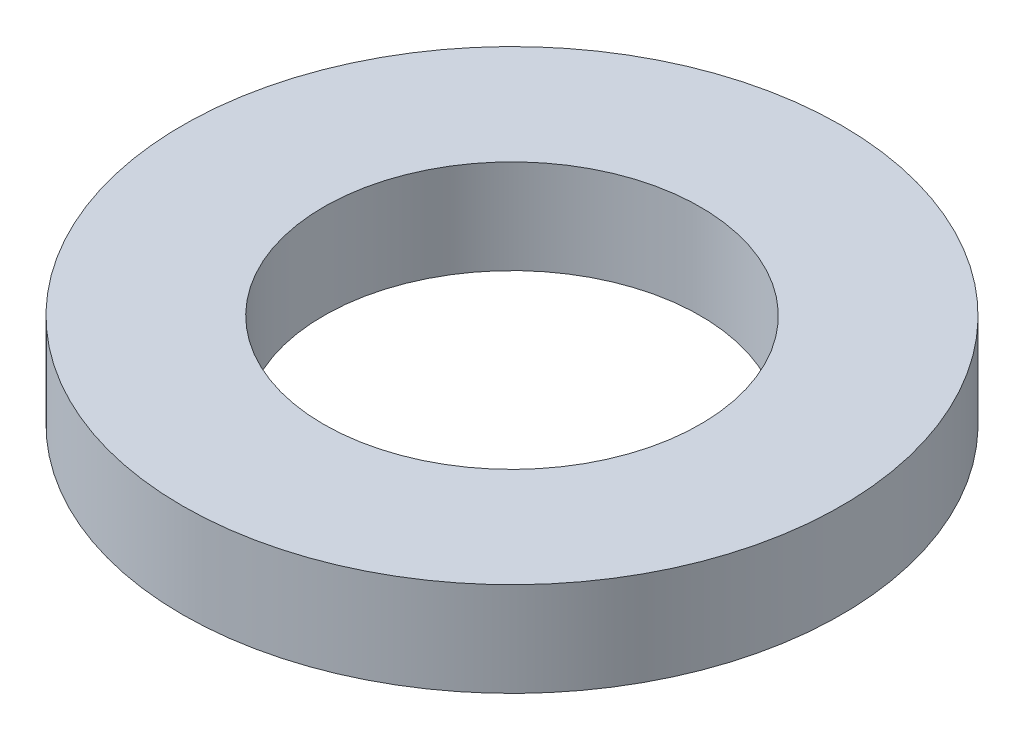
SolidWorks part; units mm, degrees
ref_plane "Спереди" through (0, 0, 0) normal (0, 0, 1) x (1, 0, 0)
ref_plane "Сверху" through (0, 0, 0) normal (0, 1, 0) x (1, 0, 0)
ref_plane "Справа" through (0, 0, 0) normal (1, 0, 0) x (0, 0, -1)
sketch "Эскиз1" plane through (0, 0, 0) normal (0, 1, 0) x (1, 0, 0)
  circle A0 centre (0, 0) radius 7
  circle A1 centre (0, 0) radius 4
  dimension "D1" = 14
  dimension "D2" = 8
extrude "Бобышка-Вытянуть1" add sketch "Эскиз1" along normal blind 2
